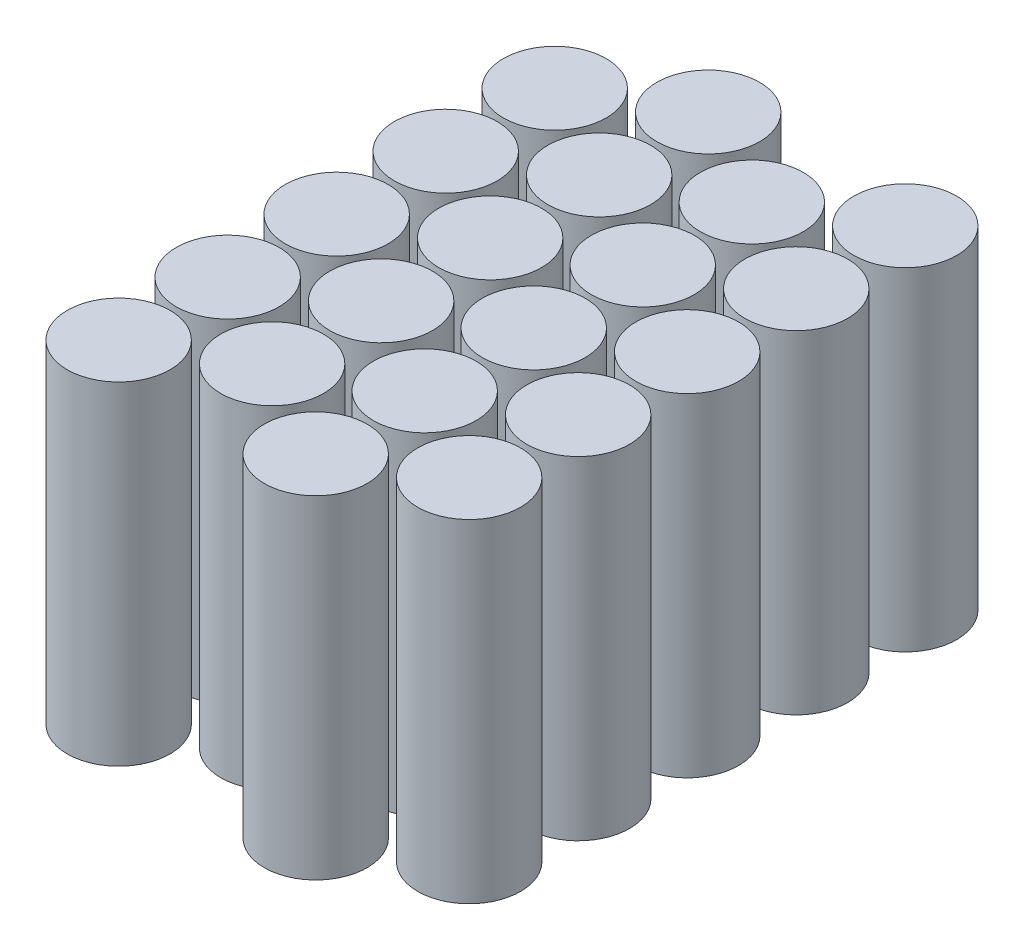
SolidWorks part; units mm, degrees
material "Nickel"
ref_plane "Front Plane" through (0, 0, 0) normal (0, 0, 1) x (1, 0, 0)
ref_plane "Top Plane" through (0, 0, 0) normal (0, 1, 0) x (1, 0, 0)
ref_plane "Right Plane" through (0, 0, 0) normal (1, 0, 0) x (0, 0, -1)
sketch "Sketch1" plane through (0, 0, 0) normal (0, 1, 0) x (1, 0, 0)
  line L0 (0, 0) -> (0, 24.8473) construction
  line L1 (0, 0) -> (20, 0) construction
  line L2 (0, 0) -> (20.5248, 11.85) construction
  line L4 (0, 0) -> (0, -18.1864) construction
  circle A0 centre (0, 0) radius 10.85
  circle A11 centre (20.5248, 11.85) radius 10.85
  dimension "D1" = 21.7
  dimension "D2" = 21.7
  dimension "D3" = 60
  dimension "D4" = 2
extrude "Molicelll 21700 - 4s5p" add sketch "Sketch1" along normal mid plane 70.2
pattern_linear "LPattern1" count 5 spacing 23 along (0, 0, 1) of "Molicelll 21700 - 4s5p"
pattern_linear "LPattern2" count 2 spacing 41.57 along (1, 0, 0) of bodies 213 334 335 339 336 340 337 341 338 342
sketch "Sketch2" plane through (0, 35.1, 0) normal (0, 1, 0) x (1, 0, 0)
  line L0 (0, 22.6873) -> (20, 22.6873)
  line L5 (20, 22.6873) -> (20, -102.85)
  line L18 (20, -102.85) -> (0, -102.85)
  line L19 (0, -102.85) -> (0, 22.6873)
  line L20 (30.7217, 27.7131) -> (30.7217, -108.4278) construction
  line L22 (41.4434, -102.85) -> (61.4434, -102.85)
  line L23 (41.4434, 22.6873) -> (41.4434, -102.85)
  line L24 (61.4434, 22.6873) -> (41.4434, 22.6873)
  line L25 (61.4434, -102.85) -> (61.4434, 22.6873)
  circle A2 centre (20.5248, 11.85) radius 10.85 construction
  circle A5 centre (0, -92) radius 10.85 construction
  point P8 (62.0948, 11.85)
  point P9 (41.57, 0)
  point P10 (41.57, -92)
  point P11 (62.0948, -80.15)
  point P25 (20.2217, 11.675)
  dimension "D1" = 20
extrude "Top Bus Bar" [suppressed] add sketch "Sketch2" along normal blind 2 separate body
sketch "Sketch7" [suppressed] plane through (0, -35.1, 0) normal (0, -1, 0) x (1, 0, 0)
  line L1 (-10.0042, -22.1353) -> (9.9958, -22.1353)
  line L2 (-10.0042, -22.1353) -> (-10.0042, 102.8647)
  line L3 (-10.0042, 102.8647) -> (9.9958, 102.8647)
  line L4 (9.9958, -22.1353) -> (9.9958, 102.8647)
  line L7 (51.7958, -22.1353) -> (71.7958, -22.1353)
  line L8 (51.7958, -22.1353) -> (51.7958, 102.8647)
  line L9 (51.7958, 102.8647) -> (71.7958, 102.8647)
  line L10 (71.7958, -22.1353) -> (71.7958, 102.8647)
  line L16 (0, 102.85) -> (0, -22.6873) construction
  line L17 (20.8958, 102.825) -> (40.8958, 102.825)
  line L18 (20.8958, 102.825) -> (20.8958, -22.175)
  line L19 (20.8958, -22.175) -> (40.8958, -22.175)
  line L20 (40.8958, 102.825) -> (40.8958, -22.175)
  point P5 (-0.0042, 102.8647)
  point P6 (61.7958, 102.8647)
  point P14 (30.8958, -22.175)
  point P15 (30.8958, 102.825)
  dimension "D1" = 20
  dimension "D2" = 20
  dimension "D3" = 125
  dimension "D4" = 30.9
  dimension "D5" = 125
  dimension "D6" = 30.9
  dimension "D7" = 20
  dimension "D8" = 125
  dimension "D9" = 30.8958
extrude "Bottom Bus Bar" [suppressed] add sketch "Sketch7" along normal blind 2
sketch "Sketch9" [suppressed] plane through (0, 0, 102.85) normal (0, 0, 1) x (1, 0, 0)
  line L0 (30.8958, -37.1) -> (30.8958, 37.082) construction
  line L1 (-10.0042, -37.1) -> (9.9958, -37.1)
  line L2 (-10.0042, -37.1) -> (-10.0042, 7)
  line L3 (-10.0042, 7) -> (9.9958, 7)
  line L4 (9.9958, -37.1) -> (9.9958, 7)
  line L13 (40.8958, -37.1) -> (20.8958, -37.1) construction
  line L14 (71.7958, 7) -> (51.7958, 7)
  line L15 (51.7958, -37.1) -> (51.7958, 7)
  line L16 (71.7958, -37.1) -> (51.7958, -37.1)
  line L17 (71.7958, -37.1) -> (71.7958, 7)
  dimension "D1" = 7
  dimension "D2" = 20
extrude "Boss-Extrude5" [suppressed] add sketch "Sketch9" along normal blind 2 separate body contours L2 L1 L4 L3 | L14 L15 L16 L17
ref_plane "Plane1" through (0, 35.1, 0) normal (0, 1, 0) x (1, 0, 0)
sketch "Sketch11" plane through (0, 35.1, 0) normal (0, 1, 0) x (1, 0, 0)
  line L0 (10.15, 25.4046) -> (10.15, -106.3289) construction
  line L1 (51.9448, 25.4046) -> (51.9448, -106.3289) construction
  line L5 (8.5625, 22.7) -> (11.7375, 22.7)
  line L6 (8.5625, 22.7) -> (8.5625, -102.85)
  line L7 (8.5625, -102.85) -> (11.7375, -102.85)
  line L8 (11.7375, 22.7) -> (11.7375, -102.85)
  line L9 (50.3573, 22.7) -> (53.5323, 22.7)
  line L10 (50.3573, 22.7) -> (50.3573, -102.85)
  line L11 (50.3573, -102.85) -> (53.5323, -102.85)
  line L12 (53.5323, 22.7) -> (53.5323, -102.85)
  circle A5 centre (0, -23) radius 10.85 construction
  circle A6 centre (62.0948, -34.15) radius 10.85 construction
  circle A7 centre (20.5248, 11.85) radius 10.85 construction
  circle A8 centre (62.0948, 11.85) radius 10.85 construction
  point P12 (10.15, -102.85)
  point P15 (51.9448, -102.85)
  dimension "D1" = 21
  dimension "D2" = 21
  dimension "D3" = 3.175
  dimension "D4" = 125.55
  dimension "D5" = 3.175
  dimension "D6" = 125.55
extrude "Boss-Extrude6" [suppressed] add sketch "Sketch11" along normal blind 3.175
equation "\"cell_diameter\"=21.7"
equation "\"D1@Sketch1\"=\"cell_diameter\""
equation "\"cell_height\"=70.2"
equation "\"series\"= 4'number of parllel assem connected in series per stack"
equation "\"parallel\"= 5'number of cells in parallel"
equation "\"lattice\"= 60"
equation "\"s_space\"= 2 * \"cell_diameter\" * cos ( \"lattice\" )"
equation "\"p_space\"= \"cell_diameter\""
equation "\"D1@Molicelll 21700 - 4s5p\" = \"cell_height\""
equation "\"D3@LPattern2\"= \"s_space\""
equation "\"D1@LPattern2\"= \"series\" / 2"
equation "\"D4@LPattern2\"= \"p_space\""
equation "\"D2@LPattern2\"= \"parallel\""
